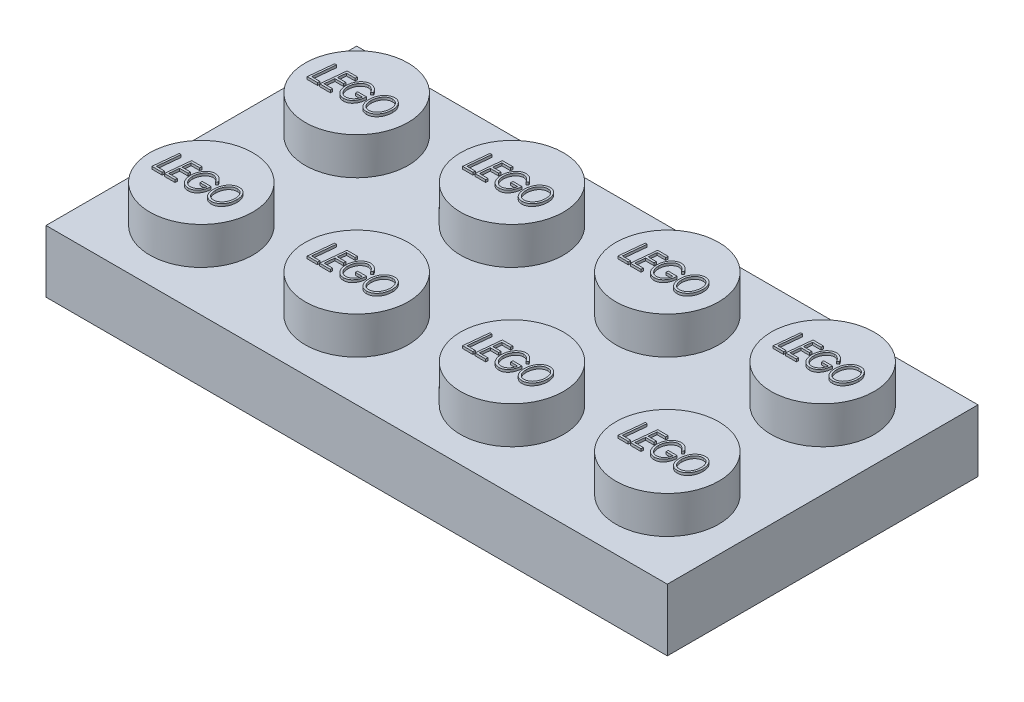
SolidWorks part; units mm, degrees
ref_plane "Front Plane" through (0, 0, 0) normal (0, 0, 1) x (1, 0, 0)
ref_plane "Top Plane" through (0, 0, 0) normal (0, 1, 0) x (1, 0, 0)
ref_plane "Right Plane" through (0, 0, 0) normal (1, 0, 0) x (0, 0, -1)
sketch "Sketch2" plane through (0, 0, 0) normal (0, 1, 0) x (1, 0, 0)
  line L0 (-33.6081, 8.7234) -> (-1.8581, 8.7234)
  line L1 (-1.8581, 8.7234) -> (-1.8581, -7.1516)
  line L2 (-1.8581, -7.1516) -> (-33.6081, -7.1516)
  line L3 (-33.6081, -7.1516) -> (-33.6081, 8.7234)
  dimension "D1" = 31.75
  dimension "D2" = 15.875
extrude "Boss-Extrude3" add sketch "Sketch2" along normal blind 3.175
sketch "Sketch3" plane through (0, 3.175, 0) normal (0, 1, 0) x (1, 0, 0)
  line L0 (-33.6081, 8.7234) -> (-33.6081, -7.1516) construction
  line L1 (-1.8581, 8.7234) -> (-33.6081, 8.7234) construction
  circle A0 centre (-29.6394, 4.7546) radius 2.6308
  dimension "D1" = 3.9687
  dimension "D2" = 3.9688
extrude "Boss-Extrude4" add sketch "Sketch3" along normal blind 1.905
pattern_linear "LPattern1" count 4 spacing 7.9375 along (1, 0, 0) count 2 spacing 7.9375 along (0, 0, 1) of "Boss-Extrude4"
shell "Shell1" thickness 1.524
sketch "Sketch4" plane through (0, 5.08, 0) normal (0, 1, 0) x (1, 0, 0)
  line L1 (-29.6394, 4.7546) -> (-29.6394, 4.0766) construction
  line L2 (-15.584, 4.0766) -> (-43.6947, 4.0766) construction
  text T0 "<i>LEGO</i>" font "Century Gothic" height 1.27
  point P2 (0, 0)
  point P4 (-13.7644, 4.7546)
  point P9 (-29.6394, 4.0766)
extrude "Boss-Extrude5" add sketch "Sketch4" along normal blind 0.127
pattern_linear "LPattern2" count 4 spacing 7.9375 along (1, 0, 0) count 2 spacing 7.9375 along (0, 0, 1) of "Boss-Extrude5"
sketch "Sketch5" plane through (0, 0, 0) normal (0, -1, 0) x (1, 0, 0)
  circle A2 centre (-9.7956, -0.7859) radius 3.175
  circle A3 centre (-9.7956, -0.7859) radius 2.3876
  dimension "D1" = 6.35
  dimension "D2" = 4.7752
extrude "Boss-Extrude6" add sketch "Sketch5" against normal up to surface (1.651 mm away) up to face at (-21.7019, 1.651, -5.8614)
pattern_linear "LPattern3" count 3 spacing 7.9375 along (-1, 0, 0) of "Boss-Extrude6"
